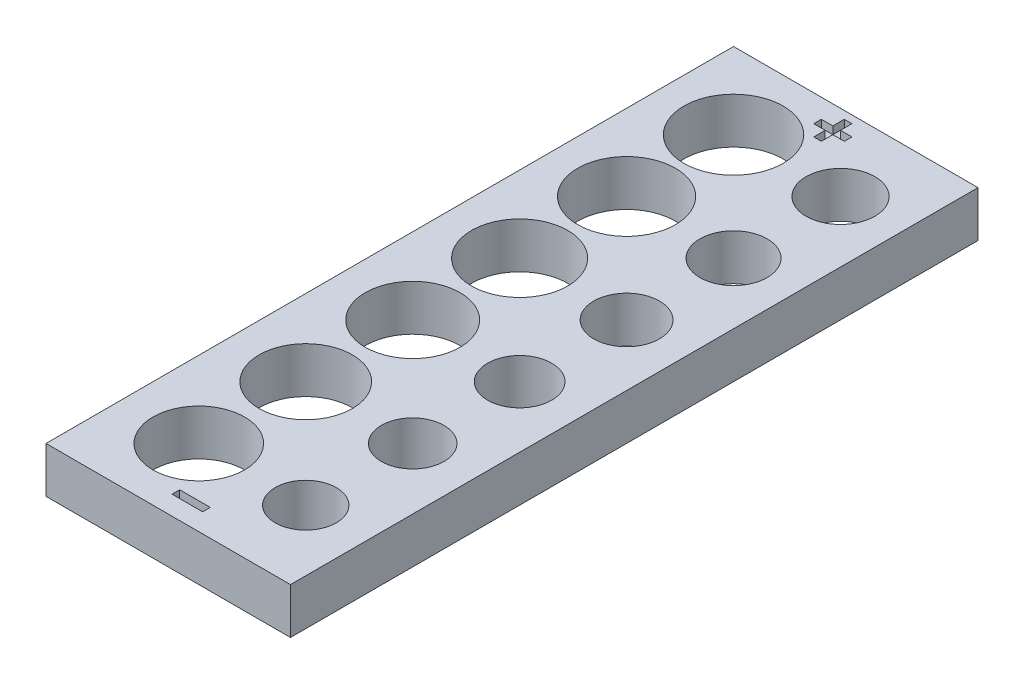
SolidWorks part; units mm, degrees
ref_plane "Front Plane" through (0, 0, 0) normal (0, 0, 1) x (1, 0, 0)
ref_plane "Top Plane" through (0, 0, 0) normal (0, 1, 0) x (1, 0, 0)
ref_plane "Right Plane" through (0, 0, 0) normal (1, 0, 0) x (0, 0, -1)
sketch "Sketch1" plane through (0, 0, 0) normal (0, 1, 0) x (1, 0, 0)
  line L0 (5, 40) -> (5, 33) construction
  line L1 (0, 0) -> (16, 0)
  line L2 (0, 0) -> (0, 45)
  line L3 (0, 45) -> (16, 45)
  line L4 (16, 0) -> (16, 45)
  line L5 (5, 33) -> (5, 26) construction
  line L6 (5, 19) -> (5, 26) construction
  line L8 (5, 5) -> (5, 12) construction
  line L9 (5, 12) -> (5, 19) construction
  circle A0 centre (5, 5) radius 3
  circle A1 centre (5, 12) radius 3.05
  circle A2 centre (5, 19) radius 3.1
  circle A3 centre (5, 26) radius 3.15
  circle A4 centre (5, 33) radius 3.2
  circle A5 centre (5, 40) radius 3.25
  circle A6 centre (12, 40) radius 2.25
  circle A7 centre (12, 33) radius 2.2
  circle A8 centre (12, 26) radius 2.15
  circle A9 centre (12, 19) radius 2.1
  circle A10 centre (12, 12) radius 2.05
  circle A11 centre (12, 5) radius 2
  point P29 (0, 0)
  point P30 (0, 0)
  point P31 (0, 0)
  point P32 (0, 0)
  point P33 (0, 0)
  point P34 (0, 0)
  point P35 (0, 0)
  dimension "D1" = 6.5
  dimension "D2" = 6.4
  dimension "D3" = 6.3
  dimension "D4" = 6.2
  dimension "D5" = 6.1
  dimension "D6" = 6
  dimension "D10" = 4.5
  dimension "D11" = 4.4
  dimension "D12" = 4.3
  dimension "D13" = 4.2
  dimension "D14" = 4.1
  dimension "D15" = 4
  dimension "D7" = 7
  dimension "D8" = 5
  dimension "D9" = 5
  dimension "D16" = 7
  dimension "D17" = 4
  dimension "D18" = 5
extrude "Boss-Extrude1" add sketch "Sketch1" along normal blind 3
sketch "Sketch2" plane through (0, 3, 0) normal (0, 1, 0) x (1, 0, 0)
  line L0 (7.75, 43.75) -> (7.75, 44.5)
  line L1 (7.75, 44.5) -> (8.25, 44.5)
  line L2 (8.25, 44.5) -> (8.25, 43.75)
  line L3 (8.25, 43.75) -> (9, 43.75)
  line L4 (9, 43.75) -> (9, 43.25)
  line L5 (9, 43.25) -> (8.25, 43.25)
  line L6 (8.25, 43.25) -> (8.25, 42.5)
  line L7 (8.25, 42.5) -> (7.75, 42.5)
  line L8 (7.75, 42.5) -> (7.75, 43.25)
  line L9 (7.75, 43.25) -> (7, 43.25)
  line L10 (7, 43.25) -> (7, 43.75)
  line L11 (7, 43.75) -> (7.75, 43.75)
  line L12 (7.75, 43.25) -> (8.25, 43.75) construction
  line L13 (0, 45) -> (16, 0) construction
  line L14 (16, 45) -> (0, 45) construction
  line L16 (7, 1.25) -> (9, 1.25)
  line L17 (7, 1.25) -> (7, 1.75)
  line L18 (7, 1.75) -> (9, 1.75)
  line L19 (9, 1.25) -> (9, 1.75)
  line L20 (7, 1.25) -> (9, 1.75) construction
  line L21 (7, 1.75) -> (9, 1.25) construction
  point P16 (8, 43.5)
  point P17 (8, 22.5)
  point P18 (8, 1.5)
  point P25 (0, 0)
  point P26 (9, 0.7261)
  dimension "D1" = 0.5
  dimension "D2" = 0.5
  dimension "D3" = 2
  dimension "D4" = 0.5
  dimension "D5" = 2
  dimension "D6" = 1.5
extrude "Cut-Extrude1" cut sketch "Sketch2" against normal blind 0.5
